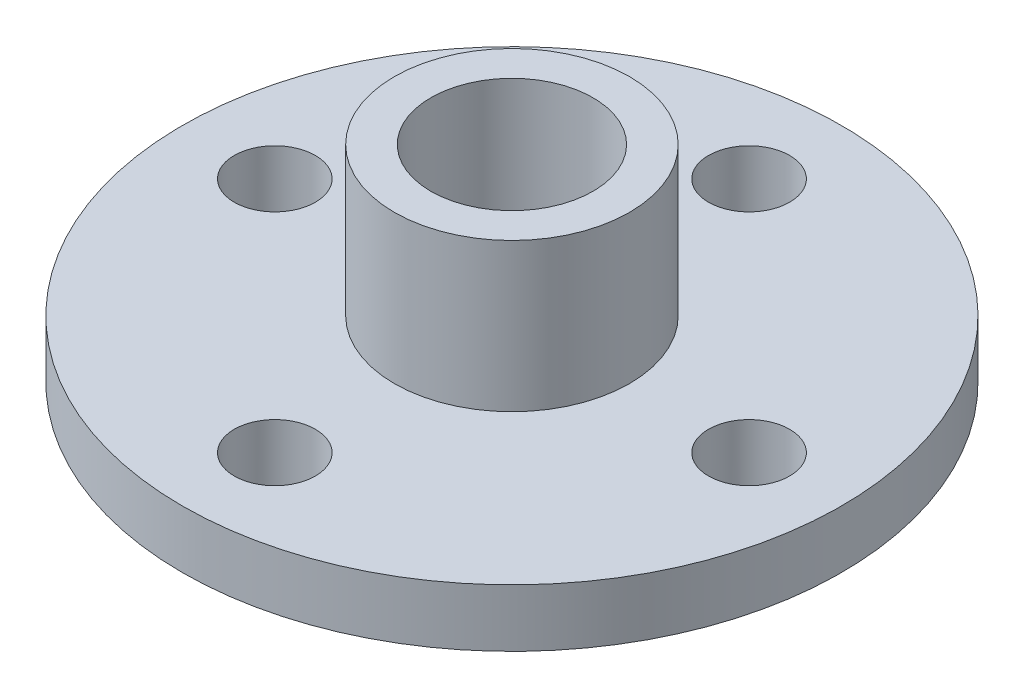
SolidWorks part; units mm, degrees
ref_plane "Front" through (0, 0, 0) normal (0, 0, 1) x (1, 0, 0)
ref_plane "Top" through (0, 0, 0) normal (0, 1, 0) x (1, 0, 0)
ref_plane "Right" through (0, 0, 0) normal (1, 0, 0) x (0, 0, -1)
sketch "Sketch1" plane through (0, 0, 0) normal (0, 1, 0) x (1, 0, 0)
  circle A3 centre (0, 0) radius 10.16
  circle A4 centre (0, 0) radius 1.625
  dimension "D1" = 3.25
  dimension "D2" = 20.32
extrude "Boss-Extrude2" add sketch "Sketch1" along normal blind 1.778
sketch "Sketch3" plane through (0, 1.778, 0) normal (0, 1, 0) x (1, 0, 0)
  circle A0 centre (0, 0) radius 3.625
  circle A1 centre (0, 0) radius 1.625 construction
  circle A2 centre (0, 0) radius 2.5
  dimension "D1" = 2
extrude "Boss-Extrude3" add sketch "Sketch3" along normal blind 4.572
sketch "Sketch4" plane through (0, 0, 0) normal (0, -1, 0) x (1, 0, 0)
  line L0 (0, 10.16) -> (0, -10.16) construction
  line L1 (-10.16, 0) -> (10.16, 0) construction
  circle A0 centre (0, 0) radius 10.16 construction
  circle A1 centre (0, 7.31) radius 1.25
  circle A2 centre (7.31, 0) radius 1.25
  circle A3 centre (-7.31, 0) radius 1.25
  circle A4 centre (0, -7.31) radius 1.25
  dimension "D2" = 2.5
  dimension "D1" = 2.85
  dimension "D3" = 2.85
  dimension "D4" = 2.85
  dimension "D5" = 2.85
extrude "Cut-Extrude1" cut sketch "Sketch4" against normal through all contours A3 | A1 | A2 | A4
